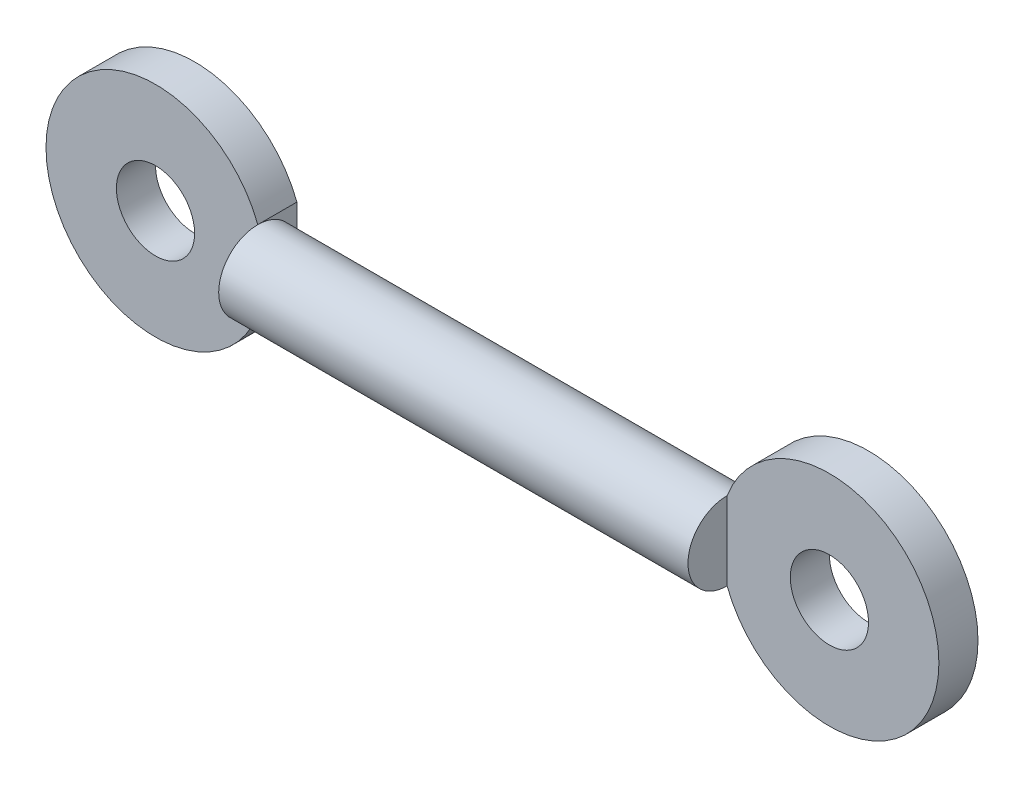
SolidWorks part; units mm, degrees
ref_plane "Front Plane" through (0, 0, 0) normal (0, 0, 1) x (1, 0, 0)
ref_plane "Top Plane" through (0, 0, 0) normal (0, 1, 0) x (1, 0, 0)
ref_plane "Right Plane" through (0, 0, 0) normal (1, 0, 0) x (0, 0, -1)
sketch "Sketch1" plane through (0, 0, 0) normal (0, 0, 1) x (1, 0, 0)
  line L0 (-15, 0) -> (15, 0)
  point P3 (0, 0)
  dimension "D1" = 30
revolve "Revolve-Thin1" add sketch "Sketch1" angle 360 about L0 wall 2.5
sketch "Sketch3" plane through (0, 0, 0) normal (0, 0, 1) x (1, 0, 0)
  line L0 (15, 2.5) -> (15, -2.5)
  line L1 (-15, -2.5) -> (-15, 2.5)
  arc A0 (15, 2.5) -> (15, -2.5) centre (21.5383, 0) cw
  arc A1 (-15, 2.5) -> (-15, -2.5) centre (-21.5383, 0) ccw
  circle A2 centre (-21.5383, 0) radius 2.5
  circle A3 centre (21.5383, 0) radius 2.5
  dimension "D1" = 7
  dimension "D2" = 5
extrude "Boss-Extrude2" add sketch "Sketch3" against normal blind 2.5
